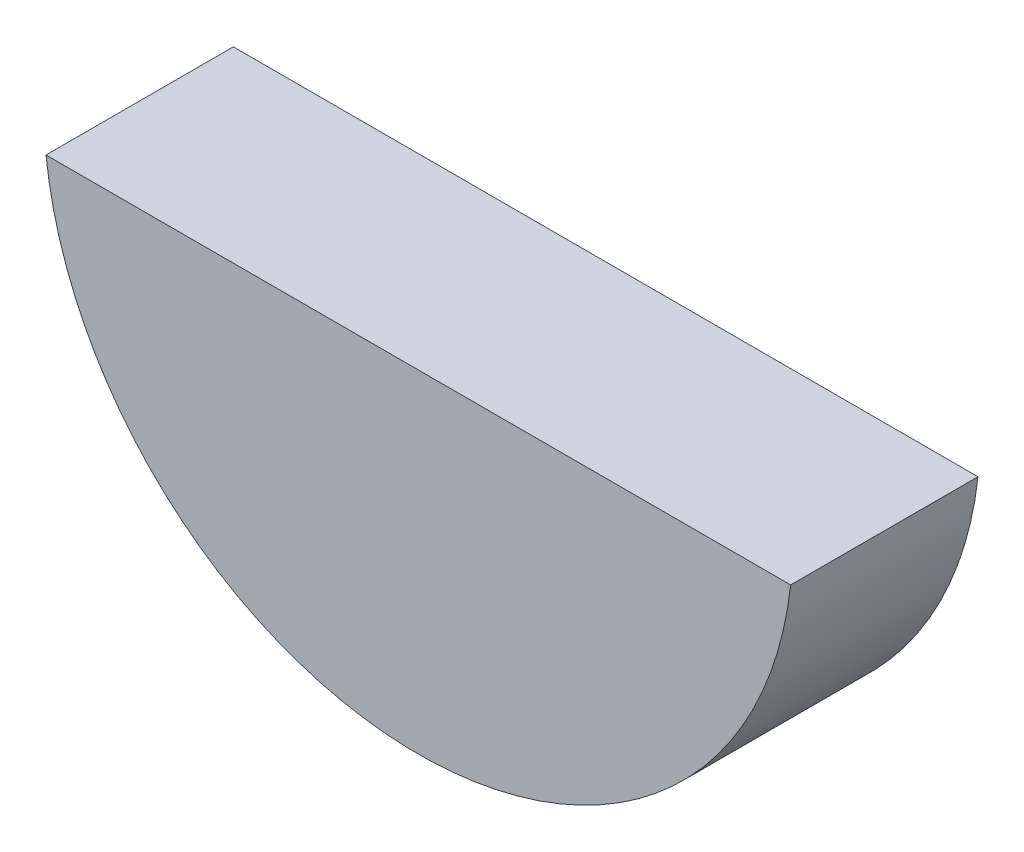
SolidWorks part; units mm, degrees
ref_plane "Front Plane" through (0, 0, 0) normal (0, 0, 1) x (1, 0, 0)
ref_plane "Top Plane" through (0, 0, 0) normal (0, 1, 0) x (1, 0, 0)
ref_plane "Right Plane" through (0, 0, 0) normal (1, 0, 0) x (0, 0, -1)
sketch "Sketch1" plane through (0, 0, 0) normal (0, 0, 1) x (1, 0, 0)
  circle A0 centre (0, 0) radius 3.175
extrude "Extrude1" add sketch "Sketch1" along normal blind 1.5875
sketch "Sketch2" plane through (0, 0, 1.5875) normal (0, 0, 1) x (1, 0, 0)
  line L0 (0, 0) -> (0, -0.3556) construction
  line L1 (0, -0.3556) -> (3.0742, -0.3556) construction
  line L3 (-3.1551, -0.3552) -> (3.1551, -0.3552)
  circle A0 centre (0, 0) radius 3.175 construction
  arc A3 (-3.1551, -0.3552) -> (3.1551, -0.3552) centre (0, 0) cw
extrude "Extrude2" cut sketch "Sketch2" against normal through all
